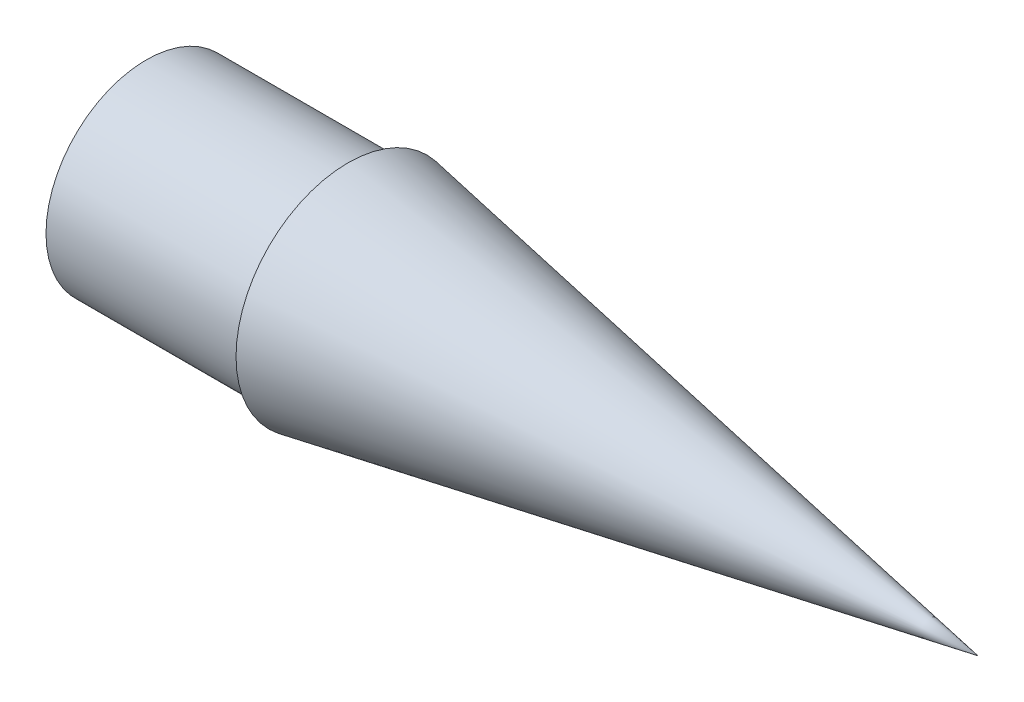
SolidWorks part; units mm, degrees
ref_plane "Front Plane" through (0, 0, 0) normal (0, 0, 1) x (1, 0, 0)
ref_plane "Top Plane" through (0, 0, 0) normal (0, 1, 0) x (1, 0, 0)
ref_plane "Right Plane" through (0, 0, 0) normal (1, 0, 0) x (0, 0, -1)
sketch "Sketch1" plane through (0, 0, 0) normal (0, 1, 0) x (1, 0, 0)
  line L0 (0, 0) -> (0, 25.273)
  line L1 (0, 25.273) -> (50.8, 25.273)
  line L2 (50.8, 25.273) -> (50.8, 28.194)
  line L3 (0, 0) -> (209.55, 0)
  line L4 (50.8, 28.194) -> (209.55, 0)
  dimension "D1" = 50.8
  dimension "D2" = 209.55
  dimension "D3" = 25.273
  dimension "D4" = 2.921
revolve "Revolve2" add sketch "Sketch1" angle 360 about L3
shell "Shell1" thickness 2.54
